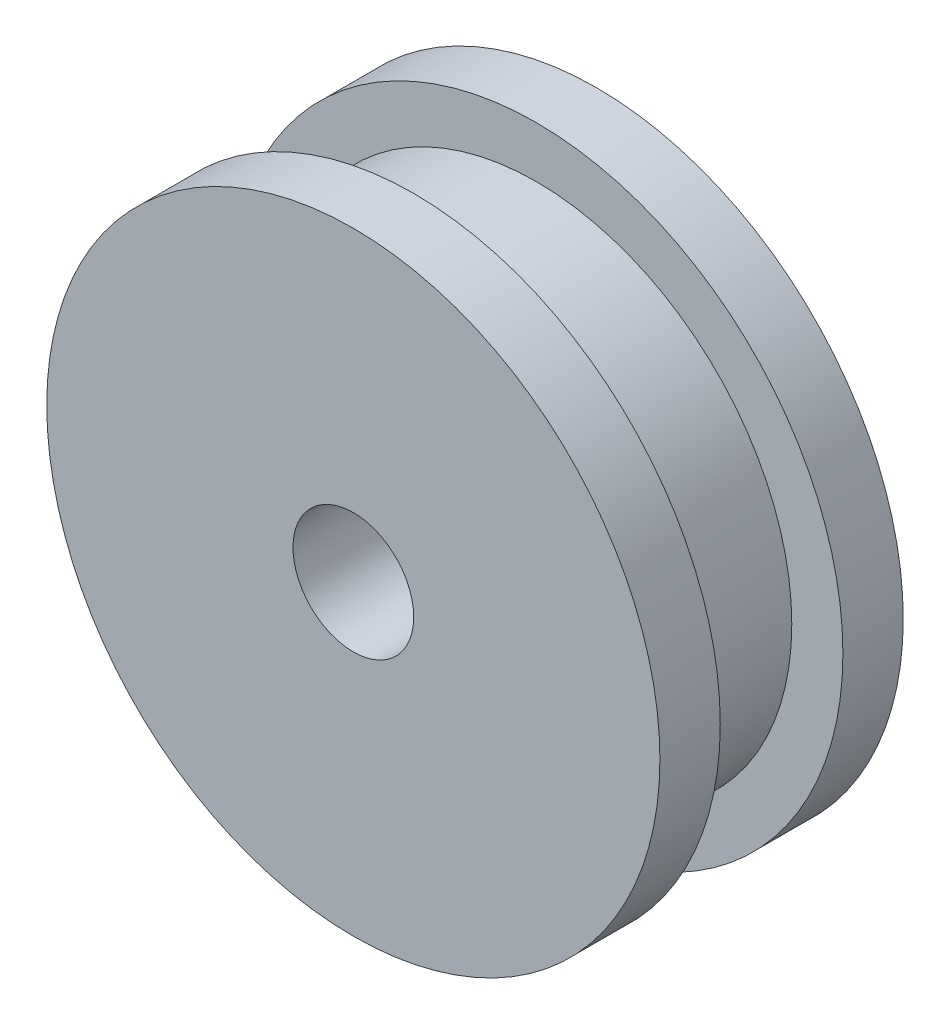
SolidWorks part; units mm, degrees
ref_plane "Front Plane" through (0, 0, 0) normal (0, 0, 1) x (1, 0, 0)
ref_plane "Top Plane" through (0, 0, 0) normal (0, 1, 0) x (1, 0, 0)
ref_plane "Right Plane" through (0, 0, 0) normal (1, 0, 0) x (0, 0, -1)
sketch "Sketch1" plane through (0, 0, 0) normal (0, 0, 1) x (1, 0, 0)
  circle A0 centre (0, 0) radius 12.7
  dimension "D1" = 25.4
extrude "Boss-Extrude1" add sketch "Sketch1" along normal mid plane 6.096
sketch "Sketch2" plane through (0, 0, 3.048) normal (0, 0, 1) x (1, 0, 0)
  circle A0 centre (0, 0) radius 15.24
  dimension "D1" = 30.48
extrude "Boss-Extrude2" add sketch "Sketch2" along normal blind 3
mirror "Mirror1" about plane through (0, 0, 0) normal (0, 0, 1) of "Boss-Extrude2"
sketch "Sketch3" plane through (0, 0, 6.048) normal (0, 0, 1) x (1, 0, 0)
  circle A0 centre (0, 0) radius 3
  dimension "D1" = 6
extrude "Cut-Extrude1" cut sketch "Sketch3" against normal blind 25.606
